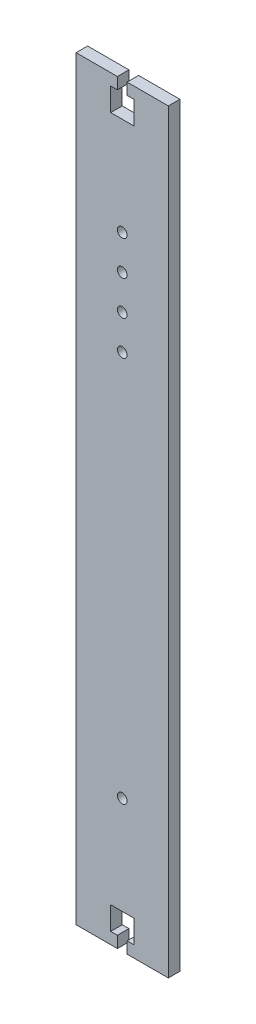
SolidWorks part; units mm, degrees
ref_plane "Front Plane" through (0, 0, 0) normal (0, 0, 1) x (1, 0, 0)
ref_plane "Top Plane" through (0, 0, 0) normal (0, 1, 0) x (1, 0, 0)
ref_plane "Right Plane" through (0, 0, 0) normal (1, 0, 0) x (0, 0, -1)
sketch "Sketch1" plane through (0, 0, 0) normal (0, 0, 1) x (1, 0, 0)
  line L0 (0, 0) -> (0, 327.5)
  line L1 (0, 0) -> (-40, 0)
  line L2 (0, 327.5) -> (-40, 327.5)
  line L3 (-40, 0) -> (-40, 327.5)
  dimension "D1" = 40
  dimension "D2" = 327.5
extrude "Boss-Extrude1" add sketch "Sketch1" along normal blind 5
sketch "Sketch2" plane through (0, 0, 0) normal (0, 0, -1) x (-1, 0, 0)
  line L0 (40, 0) -> (0, 0) construction
  line L1 (40, 327.5) -> (40, 0) construction
  line L2 (0, 327.5) -> (40, 327.5) construction
  circle A0 centre (20, 57.5) radius 2.1
  circle A1 centre (20, 270) radius 2.1
  circle A2 centre (20, 255) radius 2.1
  circle A3 centre (20, 240) radius 2.1
  circle A4 centre (20, 225) radius 2.1
  circle A5 centre (20, 210) radius 2.1 construction
  circle A6 centre (20, 195) radius 2.1 construction
  circle A7 centre (20, 180) radius 2.1 construction
  circle A8 centre (20, 165) radius 2.1 construction
  circle A9 centre (20, 150) radius 2.1 construction
  circle A10 centre (20, 135) radius 2.1 construction
  dimension "D1" = 4.2
  dimension "D2" = 57.5
  dimension "D3" = 20
  dimension "D4" = 57.5
  dimension "D5" = 4.2
  dimension "D6" = 20
  dimension "D7" = 10
extrude "Cut-Extrude1" cut sketch "Sketch2" against normal blind 5
sketch "Sketch3" plane through (0, 0, 0) normal (0, 0, -1) x (-1, 0, 0)
  line L0 (40, 0) -> (0, 0) construction
  line L1 (22.1, 0) -> (17.9, 0)
  line L2 (22.1, 0) -> (22.1, 5)
  line L3 (22.1, 5) -> (17.9, 5)
  line L4 (17.9, 0) -> (17.9, 5)
  line L5 (0, 163.75) -> (11.4243, 163.75) construction
  line L6 (15, 5) -> (25, 5)
  line L7 (15, 5) -> (15, 15)
  line L8 (15, 15) -> (25, 15)
  line L9 (25, 5) -> (25, 15)
  line L10 (0, 0) -> (0, 327.5) construction
  line L11 (25, 322.5) -> (25, 312.5)
  line L12 (15, 312.5) -> (25, 312.5)
  line L13 (15, 322.5) -> (15, 312.5)
  line L14 (15, 322.5) -> (25, 322.5)
  line L15 (17.9, 327.5) -> (17.9, 322.5)
  line L16 (22.1, 322.5) -> (17.9, 322.5)
  line L17 (22.1, 327.5) -> (22.1, 322.5)
  line L18 (22.1, 327.5) -> (17.9, 327.5)
  point P10 (20, 15)
  point P11 (20, 0)
  point P12 (20, 5)
  point P13 (20, 5)
  dimension "D1" = 10
  dimension "D2" = 5
  dimension "D3" = 10
  dimension "D4" = 4.2
extrude "Cut-Extrude2" cut sketch "Sketch3" against normal blind 5 contours L6 L9 L8 L7 L3
ref_plane "Plane1" through (0, 163.75, 0) normal (0, 1, 0) x (1, 0, 0)
mirror "Mirror1" about plane through (0, 163.75, 0) normal (0, 1, 0) of "Cut-Extrude2"
sketch "Sketch4" plane through (0, 0, 5) normal (0, 0, 1) x (1, 0, 0)
  line L0 (0, 0) -> (0, 327.5) construction
  line L1 (-15, 30) -> (-10, 30)
  line L2 (-15, 30) -> (-15, 10)
  line L3 (-15, 10) -> (-10, 10)
  line L4 (-10, 30) -> (-10, 10)
  line L6 (-17.9, 0) -> (0, 0) construction
  dimension "D1" = 5
  dimension "D2" = 10
  dimension "D3" = 20
  dimension "D4" = 10
extrude "Cut-Extrude3" [suppressed] cut sketch "Sketch4" against normal blind 10
